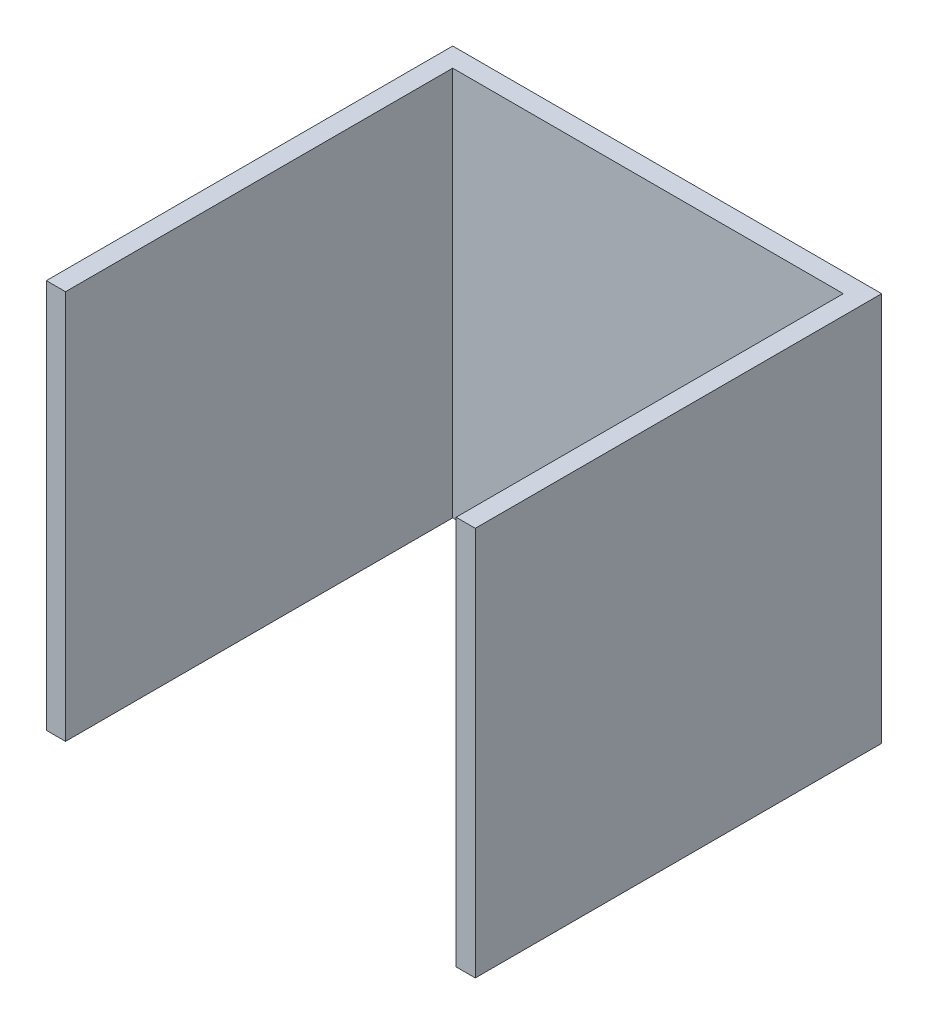
SolidWorks part; units mm, degrees
ref_plane "Front Plane" through (0, 0, 0) normal (0, 0, 1) x (1, 0, 0)
ref_plane "Top Plane" through (0, 0, 0) normal (0, 1, 0) x (1, 0, 0)
ref_plane "Right Plane" through (0, 0, 0) normal (1, 0, 0) x (0, 0, -1)
sketch "Sketch2" plane through (0, 0, 0) normal (0, 1, 0) x (1, 0, 0)
  line L0 (17, 0) -> (17, 343)
  line L2 (0, 0) -> (0, 360)
  line L3 (0, 360) -> (380, 360)
  line L4 (380, 0) -> (380, 360)
  line L5 (17, 343) -> (363, 343)
  line L6 (363, 0) -> (363, 343)
  line L7 (0, 0) -> (17, 0)
  line L8 (363, 0) -> (380, 0)
  dimension "D1" = 360
  dimension "D2" = 380
  dimension "D3" = 360
  dimension "D4" = 17
extrude "Boss-Extrude1" add sketch "Sketch2" along normal blind 345
